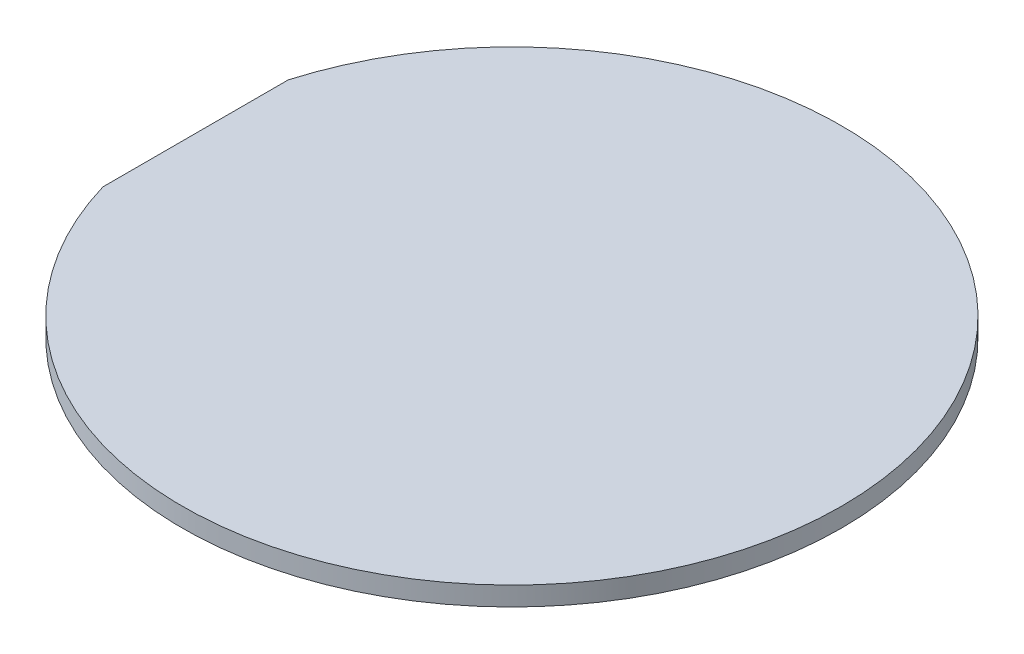
SolidWorks part; units mm, degrees
ref_plane "前视基准面" through (0, 0, 0) normal (0, 0, 1) x (1, 0, 0)
ref_plane "上视基准面" through (0, 0, 0) normal (0, 1, 0) x (1, 0, 0)
ref_plane "右视基准面" through (0, 0, 0) normal (1, 0, 0) x (0, 0, -1)
sketch "草图1" plane through (0, 0, 0) normal (0, 1, 0) x (1, 0, 0)
  circle A0 centre (0, 0) radius 15.9
  dimension "D1" = 31.8
extrude "凸台-拉伸1" add sketch "草图1" along normal blind 1
sketch "草图2" plane through (0, 1, 0) normal (0, 1, 0) x (1, 0, 0)
  circle A0 centre (0, 0) radius 17.35
  dimension "D1" = 34.7
extrude "凸台-拉伸2" add sketch "草图2" along normal blind 1
sketch "草图3" plane through (0, 1, 0) normal (0, -1, 0) x (1, 0, 0)
  line L0 (-16.65, 4.8785) -> (-16.65, -4.8785)
  circle A0 centre (0, 0) radius 17.35 construction
  arc A1 (-16.65, 4.8785) -> (-16.65, -4.8785) centre (0, 0) ccw
  dimension "D1" = 34
extrude "切除-拉伸1" cut sketch "草图3" against normal blind 1
